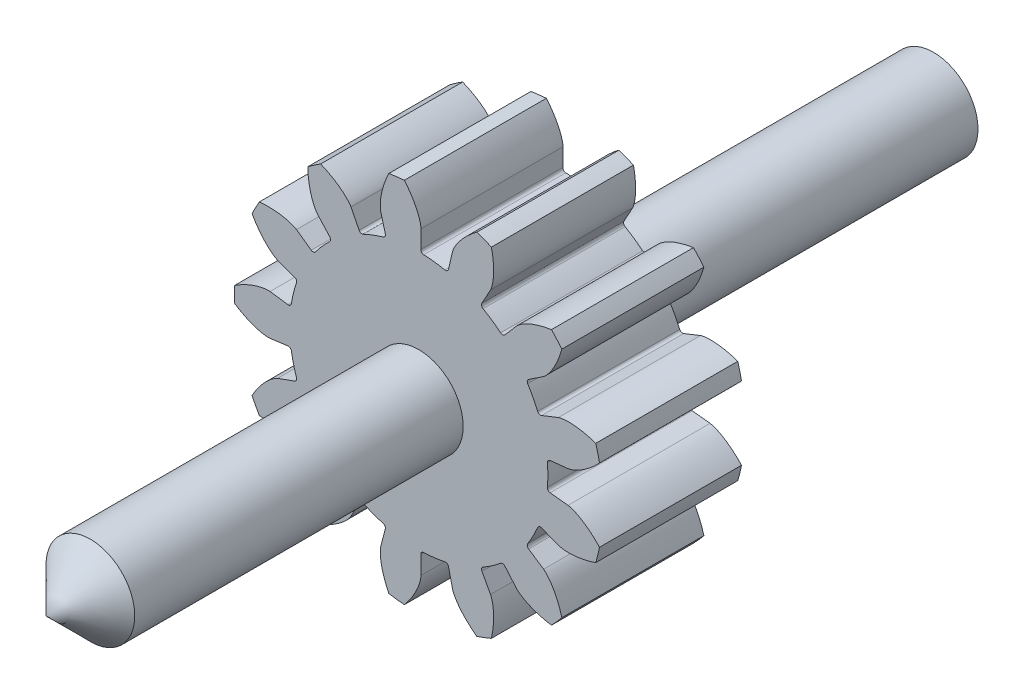
SolidWorks part; units mm, degrees
ref_plane "Front Plane" through (0, 0, 0) normal (0, 0, 1) x (1, 0, 0)
ref_plane "Top Plane" through (0, 0, 0) normal (0, 1, 0) x (1, 0, 0)
ref_plane "Right Plane" through (0, 0, 0) normal (1, 0, 0) x (0, 0, -1)
sketch "D" plane through (0, 0, 0) normal (0, 0, 1) x (1, 0, 0)
  circle A0 centre (0, 0) radius 4.5 construction
  dimension "D1" = 9
sketch "De, Di, Db" plane through (0, 0, 0) normal (0, 0, 1) x (1, 0, 0)
  circle A0 centre (0, 0) radius 4.2286 construction
  circle A1 centre (0, 0) radius 5.1923 construction
  circle A2 centre (0, 0) radius 3.6346 construction
  point P7 (0, 0)
  dimension "D1" = 8.4572
  dimension "D2" = 10.3846
  dimension "D3" = 7.2692
sketch "Sketch4" plane through (0, 0, 0) normal (0, 0, 1) x (1, 0, 0)
  circle A0 centre (0, 0) radius 5.1923 construction
  circle A1 centre (0, 0) radius 5.1923
extrude "Addendum Extruded" add sketch "Sketch4" along normal mid plane 4
sketch "Tooth Profile Curve" plane through (0, 0, 0) normal (0, 0, 1) x (1, 0, 0)
  line L0 (0, 0) -> (5.1923, 0) construction
  line L1 (0, 0) -> (4.2049, 0.4474) construction
  line L2 (0, 0) -> (4.4672, 0.5424) construction
  line L3 (4.2049, 0.4474) -> (3.6142, 0.3845)
  line L4 (3.6346, 0) -> (5.1923, 0)
  circle A0 centre (0, 0) radius 4.2286 construction
  circle A1 centre (0, 0) radius 5.1923 construction
  circle A2 centre (0, 0) radius 3.6346 construction
  circle A3 centre (0, 0) radius 4.5 construction
  arc A4 (3.6142, 0.3845) -> (3.6346, 0) centre (0, 0) cw
  arc A5 (5.1923, 0) -> (5.0896, 1.0274) centre (0, 0) ccw
  spline S0 degree 4 poles (4.2049, 0.4474) (4.208, 0.4478) (4.2167, 0.4491) (4.2329, 0.4523) (4.2593, 0.4588) (4.3076, 0.4732) (4.3646, 0.4944) (4.4276, 0.5221) (4.4938, 0.5556) (4.5494, 0.5865) (4.6039, 0.6195) (4.6573, 0.6541) (4.7208, 0.6982) (4.7952, 0.7541) (4.8796, 0.8236) (4.972, 0.9072) (5.0626, 0.9975) (5.1486, 1.0903) (5.2317, 1.1885) (5.3094, 1.2866) (5.386, 1.3927) (5.4546, 1.4929) (5.5267, 1.6095) (5.5835, 1.7049) (5.6531, 1.8352) (5.6927, 1.9135) (5.7371, 2.0065) (5.7558, 2.0486) (5.7674, 2.0745) knots 0 0 0 0 0 0.005377 0.015084 0.028532 0.04661 0.092111 0.119476 0.146842 0.174209 0.201575 0.228941 0.256307 0.307035 0.361767 0.4165 0.471232 0.525964 0.580697 0.635429 0.690161 0.744894 0.799626 0.854358 0.909091 0.954545 1 1 1 1 1 construction
  spline S1 degree 4 poles (4.2049, 0.4474) (4.208, 0.4478) (4.2167, 0.4491) (4.2329, 0.4523) (4.2593, 0.4588) (4.3076, 0.4732) (4.3646, 0.4944) (4.4276, 0.5221) (4.4938, 0.5556) (4.5494, 0.5865) (4.6039, 0.6195) (4.6573, 0.6541) (4.7208, 0.6982) (4.7952, 0.7541) (4.8796, 0.8236) (4.972, 0.9072) (5.0626, 0.9975) (5.1486, 1.0903) (5.2317, 1.1885) (5.3094, 1.2866) (5.386, 1.3927) (5.4546, 1.4929) (5.5267, 1.6095) (5.5835, 1.7049) (5.638, 1.807) (5.664, 1.8571) (5.677, 1.883) knots 0 0 0 0 0 0.005377 0.015084 0.028532 0.04661 0.092111 0.119476 0.146842 0.174209 0.201575 0.228941 0.256307 0.307035 0.361767 0.4165 0.471232 0.525964 0.580697 0.635429 0.690161 0.744894 0.799626 0.854358 0.909091 0.909091 0.909091 0.909091 0.909091
  dimension "D1" = 6.923
  dimension "D2" = 0.85
  dimension "D3" = 6.073
extrude "1/2 Tooth Cut" cut sketch "Tooth Profile Curve" against normal mid plane 4
ref_plane "Plane of Mirroring" through (0, 0, 0) normal (0, 1, 0) x (1, 0, 0)
mirror "Mirror Tooth Cut" about plane through (0, 0, 0) normal (0, 1, 0) of "1/2 Tooth Cut"
fillet "Roots Fillet" radius 0.0865 2 edges at (3.6142, -0.3845, 0) (3.6142, 0.3845, 0)
pattern_circular "Circular Pattern of Teeth" count 13 over 360 about axis through (0, 0, -2) along (0, 0, 1) of "Mirror Tooth Cut", "1/2 Tooth Cut", "Roots Fillet"
sketch "Sketch5" plane through (0, 0, 0) normal (0, 0, 1) x (1, 0, 0)
  line L0 (1, 4) -> (-1, 4) construction
  line L1 (-1, 5) -> (1, 5)
  line L2 (-1, 5) -> (-1, 3.873)
  line L5 (1, 4) -> (1, 5)
  line L6 (1, 4) -> (1, 3.873)
  arc A0 (-1, 3.873) -> (1, 3.873) centre (0, 0) ccw
  circle A1 centre (0, 0) radius 4 construction
  point P9 (0, 5)
  dimension "D1" = 8
  dimension "D2" = 1
  dimension "D3" = 2
sketch "Sketch6" [suppressed] plane through (0, 0, 0) normal (0, 0, 1) x (1, 0, 0)
  line L6 (41.8591, 5.9947) -> (34.5048, 4.9415) construction
  line L7 (37.3883, 19.7543) -> (30.8195, 16.2837) construction
  line L8 (41.8591, 5.9947) -> (34.5048, 4.9415)
  line L9 (37.3883, 19.7543) -> (30.8195, 16.2837)
  arc A14 (52.1159, 14.1398) -> (50.4738, 19.1936) centre (0, 0) ccw construction
  arc A20 (34.5048, 4.9415) -> (33.5461, 3.7044) centre (34.6643, 3.8278) ccw construction
  arc A29 (29.3167, 16.721) -> (30.8195, 16.2837) centre (30.294, 17.2784) ccw construction
  circle A30 centre (0, 0) radius 33.75 construction
  arc A31 (52.1159, 14.1398) -> (50.4738, 19.1936) centre (0, 0) ccw
  arc A32 (34.5048, 4.9415) -> (33.5461, 3.7044) centre (34.6643, 3.8278) ccw
  arc A33 (29.3167, 16.721) -> (30.8195, 16.2837) centre (30.294, 17.2784) ccw
  arc A34 (29.3167, 16.721) -> (33.5461, 3.7044) centre (0, 0) ccw
  spline S2 degree 4 poles (965.1968, -1751.9554) (49.5722, -17.509) (34.0199, 17.1415) (35.6787, 19.1473) (37.9033, 19.963) (38.3849, 20.1134) (39.1305, 20.2925) (39.9677, 20.4275) (40.8649, 20.5145) (41.6597, 20.5534) (42.2962, 20.5635) (43.0686, 20.5519) (43.9989, 20.5031) (45.0849, 20.3985) (46.322, 20.2188) (47.5725, 19.978) (64.8653, 15.8708) (78.7396, -0.7897) (70.5074, -3.2513) (1756.2094, -1025.0114) knots -0.360808 -0.360808 -0.360808 -0.360808 -0.360808 0.005377 0.015084 0.028532 0.04661 0.092111 0.146842 0.174209 0.201575 0.228941 0.256307 0.307035 0.361767 0.4165 0.471232 0.525964 3.418372 3.418372 3.418372 3.418372 3.418372 only from (37.3883, 19.7543) to (50.4738, 19.1936) construction
  spline S3 degree 4 poles (-248.913, 1984.6901) (29.8132, 43.3029) (37.5982, 6.1286) (40.1192, 5.4809) (42.3983, 6.1286) (42.8764, 6.29) (43.5848, 6.5834) (44.3415, 6.9662) (45.1185, 7.4233) (45.7844, 7.859) (46.3053, 8.2249) (46.9233, 8.6882) (47.6473, 9.2745) (48.4644, 9.9975) (49.3596, 10.87) (50.2297, 11.7999) (61.8058, 25.2872) (63.2375, 46.9208) (55.1306, 44.0736) (818.3166, 1861.5256) knots -0.360808 -0.360808 -0.360808 -0.360808 -0.360808 0.005377 0.015084 0.028532 0.04661 0.092111 0.146842 0.174209 0.201575 0.228941 0.256307 0.307035 0.361767 0.4165 0.471232 0.525964 3.418372 3.418372 3.418372 3.418372 3.418372 only from (41.8591, 5.9947) to (52.1159, 14.1398) construction
  spline S4 degree 4 poles (37.3883, 19.7543) (37.4162, 19.7684) (37.4955, 19.8059) (37.6488, 19.8697) (37.9033, 19.963) (38.3849, 20.1134) (39.1305, 20.2925) (39.9677, 20.4275) (40.8649, 20.5145) (41.6597, 20.5534) (42.2962, 20.5635) (43.0686, 20.5519) (43.9989, 20.5031) (45.0849, 20.3985) (46.322, 20.2188) (47.5725, 19.978) (48.7682, 19.694) (49.6459, 19.4492) (50.2125, 19.2764) (50.4738, 19.1936) knots 0 0 0 0 0 0.005377 0.015084 0.028532 0.04661 0.092111 0.146842 0.174209 0.201575 0.228941 0.256307 0.307035 0.361767 0.4165 0.471232 0.525964 0.573123 0.573123 0.573123 0.573123 0.573123
  spline S5 degree 4 poles (41.8591, 5.9947) (41.8899, 5.9998) (41.9761, 6.016) (42.1376, 6.0545) (42.3983, 6.1286) (42.8764, 6.29) (43.5848, 6.5834) (44.3415, 6.9662) (45.1185, 7.4233) (45.7844, 7.859) (46.3053, 8.2249) (46.9233, 8.6882) (47.6473, 9.2745) (48.4644, 9.9975) (49.3596, 10.87) (50.2297, 11.7999) (51.0302, 12.7325) (51.5963, 13.4464) (51.9531, 13.9192) (52.1159, 14.1398) knots 0 0 0 0 0 0.005377 0.015084 0.028532 0.04661 0.092111 0.146842 0.174209 0.201575 0.228941 0.256307 0.307035 0.361767 0.4165 0.471232 0.525964 0.573123 0.573123 0.573123 0.573123 0.573123
extrude "Teeth Removing" [suppressed] cut sketch "Sketch6" against normal through all both flip side to cut
sketch "Sketch7" [suppressed] plane through (0, 0, 0) normal (0, 0, 1) x (1, 0, 0)
  line L0 (-3, 10) -> (3, 10)
  line L1 (3, 10) -> (3, 7.4162)
  line L2 (-3, 10) -> (-3, 7.4162)
  arc A0 (-3, 7.4162) -> (3, 7.4162) centre (0, 0) ccw
  point P1 (0, 10)
  dimension "D1" = 8
  dimension "D2" = 10
  dimension "D3" = 6
extrude "Cut-Extrude1" [suppressed] cut sketch "Sketch7" against normal through all both and the other way through all
sketch "Sketch8" [suppressed] plane through (0, 0, 0) normal (0, 0, 1) x (1, 0, 0)
  line L0 (-4.8226, 27.7752) -> (-3.9753, 22.8953) construction
  line L1 (4.8226, 27.7752) -> (3.9753, 22.8953) construction
  line L2 (-4.8226, 27.7752) -> (-3.9753, 22.8953)
  line L3 (4.8226, 27.7752) -> (3.9753, 22.8953)
  arc A0 (-4.5622, 22.0326) -> (4.5622, 22.0326) centre (0, 0) ccw
  arc A1 (-4.5622, 22.0326) -> (-3.9753, 22.8953) centre (-4.7142, 22.767) ccw construction
  arc A2 (3.9753, 22.8953) -> (4.5622, 22.0326) centre (4.7142, 22.767) ccw construction
  arc A3 (-4.5622, 22.0326) -> (-3.9753, 22.8953) centre (-4.7142, 22.767) ccw
  arc A4 (3.9753, 22.8953) -> (4.5622, 22.0326) centre (4.7142, 22.767) ccw
  arc A5 (-1.7713, 35.9564) -> (1.7713, 35.9564) centre (0, 0) cw
  spline S0 degree 4 poles (-2951.1447, 536.0596) (-42.0553, 30.3098) (3.4186, 24.472) (4.7778, 26.2412) (4.8488, 28.1447) (4.8449, 28.481) (4.8049, 28.9907) (4.718, 29.5493) (4.5883, 30.1361) (4.4492, 30.6481) (4.3245, 31.0537) (4.1581, 31.541) (3.9355, 32.1209) (3.6454, 32.7879) (3.2766, 33.5352) (2.8663, 34.2784) (-4.9345, 47.0779) (-24.4948, 52.3174) (-14.1166, 37.6796) (-2283.6828, 1979.2083) knots -0.444693 -0.444693 -0.444693 -0.444693 -0.444693 0.005377 0.015084 0.028532 0.04661 0.092111 0.146842 0.174209 0.201575 0.228941 0.256307 0.307035 0.361767 0.4165 0.471232 0.525964 4.228351 4.228351 4.228351 4.228351 4.228351 only from (4.8226, 27.7752) to (1.7713, 35.9564) construction
  spline S1 degree 4 poles (2951.1447, 536.0596) (42.0553, 30.3098) (-3.4186, 24.472) (-4.7778, 26.2412) (-4.8488, 28.1447) (-4.8449, 28.481) (-4.8049, 28.9907) (-4.718, 29.5493) (-4.5883, 30.1361) (-4.4492, 30.6481) (-4.3245, 31.0537) (-4.1581, 31.541) (-3.9355, 32.1209) (-3.6454, 32.7879) (-3.2766, 33.5352) (-2.8663, 34.2784) (4.9345, 47.0779) (24.4948, 52.3174) (14.1166, 37.6796) (2283.6828, 1979.2083) knots -0.444693 -0.444693 -0.444693 -0.444693 -0.444693 0.005377 0.015084 0.028532 0.04661 0.092111 0.146842 0.174209 0.201575 0.228941 0.256307 0.307035 0.361767 0.4165 0.471232 0.525964 4.228351 4.228351 4.228351 4.228351 4.228351 only from (-4.8226, 27.7752) to (-1.7713, 35.9564) construction
  spline S2 degree 4 poles (4.8226, 27.7752) (4.8257, 27.7958) (4.8332, 27.8538) (4.842, 27.9641) (4.8488, 28.1447) (4.8449, 28.481) (4.8049, 28.9907) (4.718, 29.5493) (4.5883, 30.1361) (4.4492, 30.6481) (4.3245, 31.0537) (4.1581, 31.541) (3.9355, 32.1209) (3.6454, 32.7879) (3.2766, 33.5352) (2.8663, 34.2784) (2.4399, 34.9781) (2.1039, 35.4841) (1.8776, 35.8078) (1.7713, 35.9564) knots 0 0 0 0 0 0.005377 0.015084 0.028532 0.04661 0.092111 0.146842 0.174209 0.201575 0.228941 0.256307 0.307035 0.361767 0.4165 0.471232 0.525964 0.573122 0.573122 0.573122 0.573122 0.573122
  spline S3 degree 4 poles (-4.8226, 27.7752) (-4.8257, 27.7958) (-4.8332, 27.8538) (-4.842, 27.9641) (-4.8488, 28.1447) (-4.8449, 28.481) (-4.8049, 28.9907) (-4.718, 29.5493) (-4.5883, 30.1361) (-4.4492, 30.6481) (-4.3245, 31.0537) (-4.1581, 31.541) (-3.9355, 32.1209) (-3.6454, 32.7879) (-3.2766, 33.5352) (-2.8663, 34.2784) (-2.4399, 34.9781) (-2.1039, 35.4841) (-1.8776, 35.8078) (-1.7713, 35.9564) knots 0 0 0 0 0 0.005377 0.015084 0.028532 0.04661 0.092111 0.146842 0.174209 0.201575 0.228941 0.256307 0.307035 0.361767 0.4165 0.471232 0.525964 0.573122 0.573122 0.573122 0.573122 0.573122
extrude "Cut-Extrude2" [suppressed] cut sketch "Sketch8" against normal through all both and the other way through all flip side to cut
sketch "Sketch9" [suppressed] plane through (0, 0, 0) normal (0, 0, 1) x (1, 0, 0)
  circle A0 centre (0, 0) radius 4
  dimension "D1" = 8
extrude "Cut-Extrude3" [suppressed] cut sketch "Sketch9" against normal through all both and the other way through all
sketch "Sketch10" [suppressed] plane through (0, 0, 0) normal (0, 0, 1) x (1, 0, 0)
  circle A0 centre (0, 0) radius 6
  dimension "D1" = 12
extrude "Cut-Extrude4" [suppressed] cut sketch "Sketch10" against normal through all both and the other way through all
sketch "Sketch11" [suppressed] plane through (0, 0, 0) normal (0, 0, 1) x (1, 0, 0)
  line L0 (27.9061, 3.9965) -> (23.0032, 3.2943) construction
  line L1 (24.9255, 13.1696) -> (20.5463, 10.8558) construction
  line L2 (-4.8226, 27.7752) -> (-3.9753, 22.8953) construction
  line L3 (4.8226, 27.7752) -> (3.9753, 22.8953) construction
  line L4 (27.9061, 3.9965) -> (23.0032, 3.2943)
  line L5 (24.9255, 13.1696) -> (20.5463, 10.8558)
  line L6 (-4.8226, 27.7752) -> (-3.9753, 22.8953)
  line L7 (4.8226, 27.7752) -> (3.9753, 22.8953)
  arc A0 (-4.5622, 22.0326) -> (22.3641, 2.4696) centre (0, 0) ccw
  arc A1 (19.5445, 11.1473) -> (20.5463, 10.8558) centre (20.196, 11.5189) ccw construction
  arc A2 (23.0032, 3.2943) -> (22.3641, 2.4696) centre (23.1095, 2.5519) ccw construction
  arc A4 (3.9753, 22.8953) -> (4.5622, 22.0326) centre (4.7142, 22.767) ccw construction
  arc A5 (19.5445, 11.1473) -> (20.5463, 10.8558) centre (20.196, 11.5189) ccw
  arc A6 (23.0032, 3.2943) -> (22.3641, 2.4696) centre (23.1095, 2.5519) ccw
  arc A7 (-4.5622, 22.0326) -> (-3.9753, 22.8953) centre (-4.7142, 22.767) ccw construction
  arc A8 (3.9753, 22.8953) -> (4.5622, 22.0326) centre (4.7142, 22.767) ccw
  arc A9 (19.5445, 11.1473) -> (4.5622, 22.0326) centre (0, 0) ccw
  arc A10 (-1.7713, 35.9564) -> (1.7713, 35.9564) centre (0, 0) cw
  arc A11 (33.6492, 12.7957) -> (34.7439, 9.4265) centre (0, 0) cw
  arc A12 (-4.5622, 22.0326) -> (-3.9753, 22.8953) centre (-4.7142, 22.767) ccw
  spline S0 degree 4 poles (-402.1308, 2972.3569) (15.8305, 49.3632) (24.3306, 4.311) (26.4333, 3.565) (28.2656, 4.0857) (28.5842, 4.1933) (29.0566, 4.3889) (29.561, 4.6441) (30.079, 4.9488) (30.5229, 5.2393) (30.8702, 5.4833) (31.2822, 5.7922) (31.7649, 6.183) (32.3096, 6.665) (32.9064, 7.2467) (33.4865, 7.8666) (43.2489, 19.2409) (42.1875, 39.4629) (31.4732, 25.0693) (1176.6422, 2783.5204) knots -0.444693 -0.444693 -0.444693 -0.444693 -0.444693 0.005377 0.015084 0.028532 0.04661 0.092111 0.146842 0.174209 0.201575 0.228941 0.256307 0.307035 0.361767 0.4165 0.471232 0.525964 4.228351 4.228351 4.228351 4.228351 4.228351 only from (27.9061, 3.9965) to (34.7439, 9.4265) construction
  spline S1 degree 4 poles (1421.7769, -2641.0538) (41.8221, -30.6307) (22.2178, 10.8135) (23.4804, 12.6529) (25.2689, 13.3086) (25.5899, 13.4089) (26.087, 13.5283) (26.6451, 13.6183) (27.2433, 13.6763) (27.7732, 13.7022) (28.1975, 13.709) (28.7124, 13.7013) (29.3326, 13.6688) (30.0566, 13.599) (30.8813, 13.4792) (31.715, 13.3187) (46.2986, 9.8549) (57.3261, -7.129) (40.1977, -1.782) (2588.0358, -1560.3024) knots -0.444693 -0.444693 -0.444693 -0.444693 -0.444693 0.005377 0.015084 0.028532 0.04661 0.092111 0.146842 0.174209 0.201575 0.228941 0.256307 0.307035 0.361767 0.4165 0.471232 0.525964 4.228351 4.228351 4.228351 4.228351 4.228351 only from (24.9255, 13.1696) to (33.6492, 12.7957) construction
  spline S2 degree 4 poles (2951.1447, 536.0596) (42.0553, 30.3098) (-3.4186, 24.472) (-4.7778, 26.2412) (-4.8488, 28.1447) (-4.8449, 28.481) (-4.8049, 28.9907) (-4.718, 29.5493) (-4.5883, 30.1361) (-4.4492, 30.6481) (-4.3245, 31.0537) (-4.1581, 31.541) (-3.9355, 32.1209) (-3.6454, 32.7879) (-3.2766, 33.5352) (-2.8663, 34.2784) (4.9345, 47.0779) (24.4948, 52.3174) (14.1166, 37.6796) (2283.6828, 1979.2083) knots -0.444693 -0.444693 -0.444693 -0.444693 -0.444693 0.005377 0.015084 0.028532 0.04661 0.092111 0.146842 0.174209 0.201575 0.228941 0.256307 0.307035 0.361767 0.4165 0.471232 0.525964 4.228351 4.228351 4.228351 4.228351 4.228351 only from (-4.8226, 27.7752) to (-1.7713, 35.9564) construction
  spline S3 degree 4 poles (-2951.1447, 536.0596) (-42.0553, 30.3098) (3.4186, 24.472) (4.7778, 26.2412) (4.8488, 28.1447) (4.8449, 28.481) (4.8049, 28.9907) (4.718, 29.5493) (4.5883, 30.1361) (4.4492, 30.6481) (4.3245, 31.0537) (4.1581, 31.541) (3.9355, 32.1209) (3.6454, 32.7879) (3.2766, 33.5352) (2.8663, 34.2784) (-4.9345, 47.0779) (-24.4948, 52.3174) (-14.1166, 37.6796) (-2283.6828, 1979.2083) knots -0.444693 -0.444693 -0.444693 -0.444693 -0.444693 0.005377 0.015084 0.028532 0.04661 0.092111 0.146842 0.174209 0.201575 0.228941 0.256307 0.307035 0.361767 0.4165 0.471232 0.525964 4.228351 4.228351 4.228351 4.228351 4.228351 only from (4.8226, 27.7752) to (1.7713, 35.9564) construction
  spline S4 degree 4 poles (27.9061, 3.9965) (27.9266, 3.9998) (27.9841, 4.0106) (28.0917, 4.0363) (28.2656, 4.0857) (28.5842, 4.1933) (29.0566, 4.3889) (29.561, 4.6441) (30.079, 4.9488) (30.5229, 5.2393) (30.8702, 5.4833) (31.2822, 5.7922) (31.7649, 6.183) (32.3096, 6.665) (32.9064, 7.2467) (33.4865, 7.8666) (34.0201, 8.4883) (34.3975, 8.9643) (34.6354, 9.2795) (34.7439, 9.4265) knots 0 0 0 0 0 0.005377 0.015084 0.028532 0.04661 0.092111 0.146842 0.174209 0.201575 0.228941 0.256307 0.307035 0.361767 0.4165 0.471232 0.525964 0.573122 0.573122 0.573122 0.573122 0.573122
  spline S5 degree 4 poles (24.9255, 13.1696) (24.9442, 13.1789) (24.997, 13.204) (25.0992, 13.2464) (25.2689, 13.3086) (25.5899, 13.4089) (26.087, 13.5283) (26.6451, 13.6183) (27.2433, 13.6763) (27.7732, 13.7022) (28.1975, 13.709) (28.7124, 13.7013) (29.3326, 13.6688) (30.0566, 13.599) (30.8813, 13.4792) (31.715, 13.3187) (32.5122, 13.1293) (33.0972, 12.9661) (33.475, 12.8509) (33.6492, 12.7957) knots 0 0 0 0 0 0.005377 0.015084 0.028532 0.04661 0.092111 0.146842 0.174209 0.201575 0.228941 0.256307 0.307035 0.361767 0.4165 0.471232 0.525964 0.573122 0.573122 0.573122 0.573122 0.573122
  spline S6 degree 4 poles (-4.8226, 27.7752) (-4.8257, 27.7958) (-4.8332, 27.8538) (-4.842, 27.9641) (-4.8488, 28.1447) (-4.8449, 28.481) (-4.8049, 28.9907) (-4.718, 29.5493) (-4.5883, 30.1361) (-4.4492, 30.6481) (-4.3245, 31.0537) (-4.1581, 31.541) (-3.9355, 32.1209) (-3.6454, 32.7879) (-3.2766, 33.5352) (-2.8663, 34.2784) (-2.4399, 34.9781) (-2.1039, 35.4841) (-1.8776, 35.8078) (-1.7713, 35.9564) knots 0 0 0 0 0 0.005377 0.015084 0.028532 0.04661 0.092111 0.146842 0.174209 0.201575 0.228941 0.256307 0.307035 0.361767 0.4165 0.471232 0.525964 0.573122 0.573122 0.573122 0.573122 0.573122
  spline S7 degree 4 poles (4.8226, 27.7752) (4.8257, 27.7958) (4.8332, 27.8538) (4.842, 27.9641) (4.8488, 28.1447) (4.8449, 28.481) (4.8049, 28.9907) (4.718, 29.5493) (4.5883, 30.1361) (4.4492, 30.6481) (4.3245, 31.0537) (4.1581, 31.541) (3.9355, 32.1209) (3.6454, 32.7879) (3.2766, 33.5352) (2.8663, 34.2784) (2.4399, 34.9781) (2.1039, 35.4841) (1.8776, 35.8078) (1.7713, 35.9564) knots 0 0 0 0 0 0.005377 0.015084 0.028532 0.04661 0.092111 0.146842 0.174209 0.201575 0.228941 0.256307 0.307035 0.361767 0.4165 0.471232 0.525964 0.573122 0.573122 0.573122 0.573122 0.573122
extrude "Cut-Extrude6" [suppressed] cut sketch "Sketch11" against normal through all both and the other way through all flip side to cut
sketch "Sketch12" [suppressed] plane through (0, 0, 0) normal (0, 0, 1) x (1, 0, 0)
  line L0 (-20.2274, -19.636) -> (-16.6736, -16.1861) construction
  line L1 (-12.4243, -25.3053) -> (-10.2415, -20.8593) construction
  line L2 (4.8226, 27.7752) -> (3.9753, 22.8953) construction
  line L3 (-4.8226, 27.7752) -> (-3.9753, 22.8953) construction
  line L4 (-20.2274, -19.636) -> (-16.6736, -16.1861)
  line L5 (-12.4243, -25.3053) -> (-10.2415, -20.8593)
  line L6 (4.8226, 27.7752) -> (3.9753, 22.8953)
  line L7 (-4.8226, 27.7752) -> (-3.9753, 22.8953)
  arc A0 (-9.2596, -20.5063) -> (4.5622, 22.0326) centre (0, 0) ccw
  arc A1 (-9.2596, -20.5063) -> (-10.2415, -20.8593) centre (-9.5682, -21.1899) ccw construction
  arc A2 (-16.6736, -16.1861) -> (-16.6413, -15.1432) centre (-17.196, -15.648) ccw construction
  arc A3 (-4.5622, 22.0326) -> (-3.9753, 22.8953) centre (-4.7142, 22.767) ccw construction
  arc A4 (3.9753, 22.8953) -> (4.5622, 22.0326) centre (4.7142, 22.767) ccw construction
  arc A5 (-9.2596, -20.5063) -> (-10.2415, -20.8593) centre (-9.5682, -21.1899) ccw
  arc A6 (-16.6736, -16.1861) -> (-16.6413, -15.1432) centre (-17.196, -15.648) ccw
  arc A7 (-4.5622, 22.0326) -> (-3.9753, 22.8953) centre (-4.7142, 22.767) ccw
  arc A8 (3.9753, 22.8953) -> (4.5622, 22.0326) centre (4.7142, 22.767) ccw
  arc A9 (-4.5622, 22.0326) -> (-16.6413, -15.1432) centre (0, 0) ccw
  arc A10 (1.7713, 35.9564) -> (-1.7713, 35.9564) centre (0, 0) ccw
  arc A11 (-19.7016, -30.1305) -> (-22.5676, -28.0482) centre (0, 0) cw
  spline S0 degree 4 poles (2072.4383, -2168.3207) (16.2078, -49.2406) (-17.15, -17.7889) (-19.2895, -18.4213) (-20.4658, -19.9195) (-20.6604, -20.1939) (-20.9275, -20.6297) (-21.1856, -21.1327) (-21.4256, -21.6837) (-21.614, -22.1796) (-21.7515, -22.5811) (-21.9033, -23.0732) (-22.064, -23.6731) (-22.2214, -24.3832) (-22.3623, -25.2046) (-22.4673, -26.0471) (-23.6796, -40.9873) (-10.9347, -56.7234) (-10.727, -38.7809) (684.1887, -2943.5283) knots -0.444693 -0.444693 -0.444693 -0.444693 -0.444693 0.005377 0.015084 0.028532 0.04661 0.092111 0.146842 0.174209 0.201575 0.228941 0.256307 0.307035 0.361767 0.4165 0.471232 0.525964 4.228351 4.228351 4.228351 4.228351 4.228351 only from (-20.2274, -19.636) to (-22.5676, -28.0482) construction
  spline S1 degree 4 poles (-2702.6142, 1300.958) (-51.8391, 0.1983) (-11.6186, -21.8076) (-11.5589, -24.0379) (-12.6203, -25.6196) (-12.8211, -25.8894) (-13.1531, -26.2782) (-13.5517, -26.6791) (-14.0016, -27.0776) (-14.415, -27.41) (-14.7543, -27.6649) (-15.1754, -27.9613) (-15.6963, -28.2995) (-16.323, -28.6687) (-17.0606, -29.0565) (-17.8295, -29.4166) (-31.6638, -35.1864) (-50.5681, -27.928) (-33.5681, -22.1859) (-3010.8877, -258.8981) knots -0.444693 -0.444693 -0.444693 -0.444693 -0.444693 0.005377 0.015084 0.028532 0.04661 0.092111 0.146842 0.174209 0.201575 0.228941 0.256307 0.307035 0.361767 0.4165 0.471232 0.525964 4.228351 4.228351 4.228351 4.228351 4.228351 only from (-12.4243, -25.3053) to (-19.7016, -30.1305) construction
  spline S2 degree 4 poles (2951.1447, 536.0596) (42.0553, 30.3098) (-3.4186, 24.472) (-4.7778, 26.2412) (-4.8488, 28.1447) (-4.8449, 28.481) (-4.8049, 28.9907) (-4.718, 29.5493) (-4.5883, 30.1361) (-4.4492, 30.6481) (-4.3245, 31.0537) (-4.1581, 31.541) (-3.9355, 32.1209) (-3.6454, 32.7879) (-3.2766, 33.5352) (-2.8663, 34.2784) (4.9345, 47.0779) (24.4948, 52.3174) (14.1166, 37.6796) (2283.6828, 1979.2083) knots -0.444693 -0.444693 -0.444693 -0.444693 -0.444693 0.005377 0.015084 0.028532 0.04661 0.092111 0.146842 0.174209 0.201575 0.228941 0.256307 0.307035 0.361767 0.4165 0.471232 0.525964 4.228351 4.228351 4.228351 4.228351 4.228351 only from (-4.8226, 27.7752) to (-1.7713, 35.9564) construction
  spline S3 degree 4 poles (-2951.1447, 536.0596) (-42.0553, 30.3098) (3.4186, 24.472) (4.7778, 26.2412) (4.8488, 28.1447) (4.8449, 28.481) (4.8049, 28.9907) (4.718, 29.5493) (4.5883, 30.1361) (4.4492, 30.6481) (4.3245, 31.0537) (4.1581, 31.541) (3.9355, 32.1209) (3.6454, 32.7879) (3.2766, 33.5352) (2.8663, 34.2784) (-4.9345, 47.0779) (-24.4948, 52.3174) (-14.1166, 37.6796) (-2283.6828, 1979.2083) knots -0.444693 -0.444693 -0.444693 -0.444693 -0.444693 0.005377 0.015084 0.028532 0.04661 0.092111 0.146842 0.174209 0.201575 0.228941 0.256307 0.307035 0.361767 0.4165 0.471232 0.525964 4.228351 4.228351 4.228351 4.228351 4.228351 only from (4.8226, 27.7752) to (1.7713, 35.9564) construction
  spline S4 degree 4 poles (-20.2274, -19.636) (-20.2421, -19.6508) (-20.2822, -19.6933) (-20.3542, -19.7774) (-20.4658, -19.9195) (-20.6604, -20.1939) (-20.9275, -20.6297) (-21.1856, -21.1327) (-21.4256, -21.6837) (-21.614, -22.1796) (-21.7515, -22.5811) (-21.9033, -23.0732) (-22.064, -23.6731) (-22.2214, -24.3832) (-22.3623, -25.2046) (-22.4673, -26.0471) (-22.5335, -26.8637) (-22.5591, -27.4706) (-22.5663, -27.8654) (-22.5676, -28.0482) knots 0 0 0 0 0 0.005377 0.015084 0.028532 0.04661 0.092111 0.146842 0.174209 0.201575 0.228941 0.256307 0.307035 0.361767 0.4165 0.471232 0.525964 0.573122 0.573122 0.573122 0.573122 0.573122
  spline S5 degree 4 poles (-12.4243, -25.3053) (-12.4339, -25.3238) (-12.4619, -25.3751) (-12.5196, -25.4695) (-12.6203, -25.6196) (-12.8211, -25.8894) (-13.1531, -26.2782) (-13.5517, -26.6791) (-14.0016, -27.0776) (-14.415, -27.41) (-14.7543, -27.6649) (-15.1754, -27.9613) (-15.6963, -28.2995) (-16.323, -28.6687) (-17.0606, -29.0565) (-17.8295, -29.4166) (-18.5857, -29.732) (-19.1549, -29.9439) (-19.5282, -30.0727) (-19.7016, -30.1305) knots 0 0 0 0 0 0.005377 0.015084 0.028532 0.04661 0.092111 0.146842 0.174209 0.201575 0.228941 0.256307 0.307035 0.361767 0.4165 0.471232 0.525964 0.573122 0.573122 0.573122 0.573122 0.573122
  spline S6 degree 4 poles (-4.8226, 27.7752) (-4.8257, 27.7958) (-4.8332, 27.8538) (-4.842, 27.9641) (-4.8488, 28.1447) (-4.8449, 28.481) (-4.8049, 28.9907) (-4.718, 29.5493) (-4.5883, 30.1361) (-4.4492, 30.6481) (-4.3245, 31.0537) (-4.1581, 31.541) (-3.9355, 32.1209) (-3.6454, 32.7879) (-3.2766, 33.5352) (-2.8663, 34.2784) (-2.4399, 34.9781) (-2.1039, 35.4841) (-1.8776, 35.8078) (-1.7713, 35.9564) knots 0 0 0 0 0 0.005377 0.015084 0.028532 0.04661 0.092111 0.146842 0.174209 0.201575 0.228941 0.256307 0.307035 0.361767 0.4165 0.471232 0.525964 0.573122 0.573122 0.573122 0.573122 0.573122
  spline S7 degree 4 poles (4.8226, 27.7752) (4.8257, 27.7958) (4.8332, 27.8538) (4.842, 27.9641) (4.8488, 28.1447) (4.8449, 28.481) (4.8049, 28.9907) (4.718, 29.5493) (4.5883, 30.1361) (4.4492, 30.6481) (4.3245, 31.0537) (4.1581, 31.541) (3.9355, 32.1209) (3.6454, 32.7879) (3.2766, 33.5352) (2.8663, 34.2784) (2.4399, 34.9781) (2.1039, 35.4841) (1.8776, 35.8078) (1.7713, 35.9564) knots 0 0 0 0 0 0.005377 0.015084 0.028532 0.04661 0.092111 0.146842 0.174209 0.201575 0.228941 0.256307 0.307035 0.361767 0.4165 0.471232 0.525964 0.573122 0.573122 0.573122 0.573122 0.573122
extrude "Cut-Extrude7" [suppressed] cut sketch "Sketch12" against normal through all both and the other way through all flip side to cut
sketch "Sketch13" plane through (0, 0, 0) normal (0, 0, 1) x (1, 0, 0)
  circle A0 centre (0, 0) radius 1.25
  dimension "D1" = 2.5
extrude "Boss-Extrude1" add sketch "Sketch13" along normal mid plane 25
sketch "Sketch14" plane through (0, 0, 0) normal (1, 0, 0) x (0, 0, -1)
  line L0 (-12.5, 1.25) -> (-12.5, -1.25) construction
  line L1 (-12.5, 0) -> (-12.5, -1.25)
  line L3 (-12.5, 1.25) -> (-12.5, -1.25)
  line L4 (-12.5, -1.25) -> (-2, -1.25) construction
  line L5 (-12.5, -1.25) -> (-2, -1.25)
  line L6 (-16.3005, 0) -> (-7.4754, 0) construction
  line L7 (-13.509, -1.009) -> (-13.509, 2.4548)
  line L8 (-13.509, 2.4548) -> (-10.0452, 2.4548)
  line L9 (-10.0452, 2.4548) -> (-13.509, -1.009)
  line L10 (-12.5, 1.25) -> (-12.5, 0)
  line L11 (-12.5, 1.25) -> (-11.25, 1.25)
  line L12 (-2, 1.25) -> (-12.5, 1.25) construction
  point P2 (-12.5, 0)
  dimension "D1" = 45
  dimension "D2" = 90
  dimension "D3" = 3.4638
  dimension "D4" = 1.009
revolve "Cut-Revolve4" cut sketch "Sketch14" angle 360 about L6
equation "\"D\"= \"D1@D\"'Pitch Diameter"
equation "\"m\"= 9 / 13'Module"
equation "\"z\"= \"D\" / \"m\"'Numer of Teeth"
equation "\"De\"= \"m\" * ( \"z\" + 2 )'Addendeum Diameter"
equation "\"Di\"= \"m\" * ( \"z\" - 2.5 )'Dedendum Diameter"
equation "\"Phi\"= 20'Pressure Angle"
equation "\"Db\"= \"D\" * cos ( \"Phi\" )'Base Diameter"
equation "\"k\"= \"m\"'Factor k"
equation "\"f\"= 1.25 * \"m\"'Factor f"
equation "\"Rf\"= ( \"f\" - \"k\" ) / 2'Roots Fillet"
equation "\"D1@De, Di, Db\"=\"Db\""
equation "\"D2@De, Di, Db\"=\"De\""
equation "\"D3@De, Di, Db\"=\"Di\""
equation "\"D1@Circular Pattern of Teeth\"=\"z\""
equation "\"D1@Roots Fillet\"=\"Rf\""
equation "\"Teta1\"= 360 / ( 4 * \"z\" )'Angle 1 For Tooth Cut"
equation "\"D1@Tooth Profile Curve\"=\"Teta1\""
equation "\"D3@Tooth Profile Curve\"=\"Teta1\"-\"D2@Tooth Profile Curve\""
equation "\"D1\" = \"Rf\""
